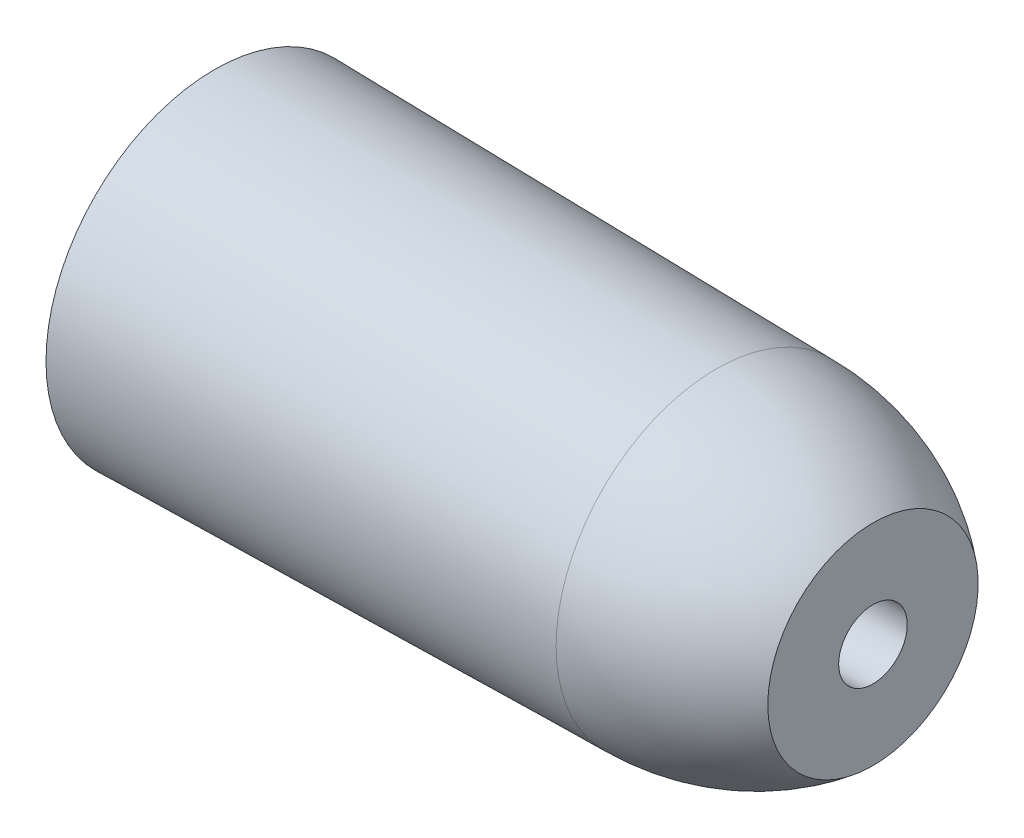
SolidWorks part; units mm, degrees
ref_plane "Front Plane" through (0, 0, 0) normal (0, 0, 1) x (1, 0, 0)
ref_plane "Top Plane" through (0, 0, 0) normal (0, 1, 0) x (1, 0, 0)
ref_plane "Right Plane" through (0, 0, 0) normal (1, 0, 0) x (0, 0, -1)
sketch "Sketch1" plane through (0, 0, 0) normal (0, 1, 0) x (1, 0, 0)
  line L0 (-491.5391, 0) -> (314.3706, 0) construction
  line L1 (-273.05, -63.9803) -> (-273.05, 63.9803)
  line L2 (-273.05, -12.3) -> (-273.05, 12.3)
  line L3 (0, -13.1) -> (0, 13.1)
  line L4 (-273.05, 12.3) -> (0, 13.1)
  line L5 (0, -13.1) -> (-273.05, -12.3)
  line L6 (-82.55, -60.7972) -> (-82.55, 60.7972)
  line L7 (-273.05, 63.9803) -> (-82.55, 60.7972)
  line L8 (-273.05, -63.9803) -> (-82.55, -60.7972)
  line L9 (-23.05, 39.9361) -> (-23.05, -39.9361)
  arc A0 (-82.55, 60.7972) -> (0, 13.1) centre (-82.55, -34.4865) cw
  arc A1 (-82.55, -60.7972) -> (0, -13.1) centre (-82.55, 34.4865) ccw
  point P6 (-273.05, 0)
  point P9 (-273.05, 0)
  point P12 (0, 0)
  point P15 (-82.55, 0)
  point P17 (-82.55, -12.8581)
  point P18 (-82.55, 12.8581)
  point P19 (-23.05, 0)
  point P23 (-23.05, 0)
  dimension "D1" = 127.9606
  dimension "D2" = 273.05
  dimension "D3" = 24.6
  dimension "D4" = 26.2
  dimension "D5" = 190.5
  dimension "D6" = 121.5944
  dimension "D7" = 250
revolve "Revolve1" add sketch "Sketch1" angle 360 about L0
